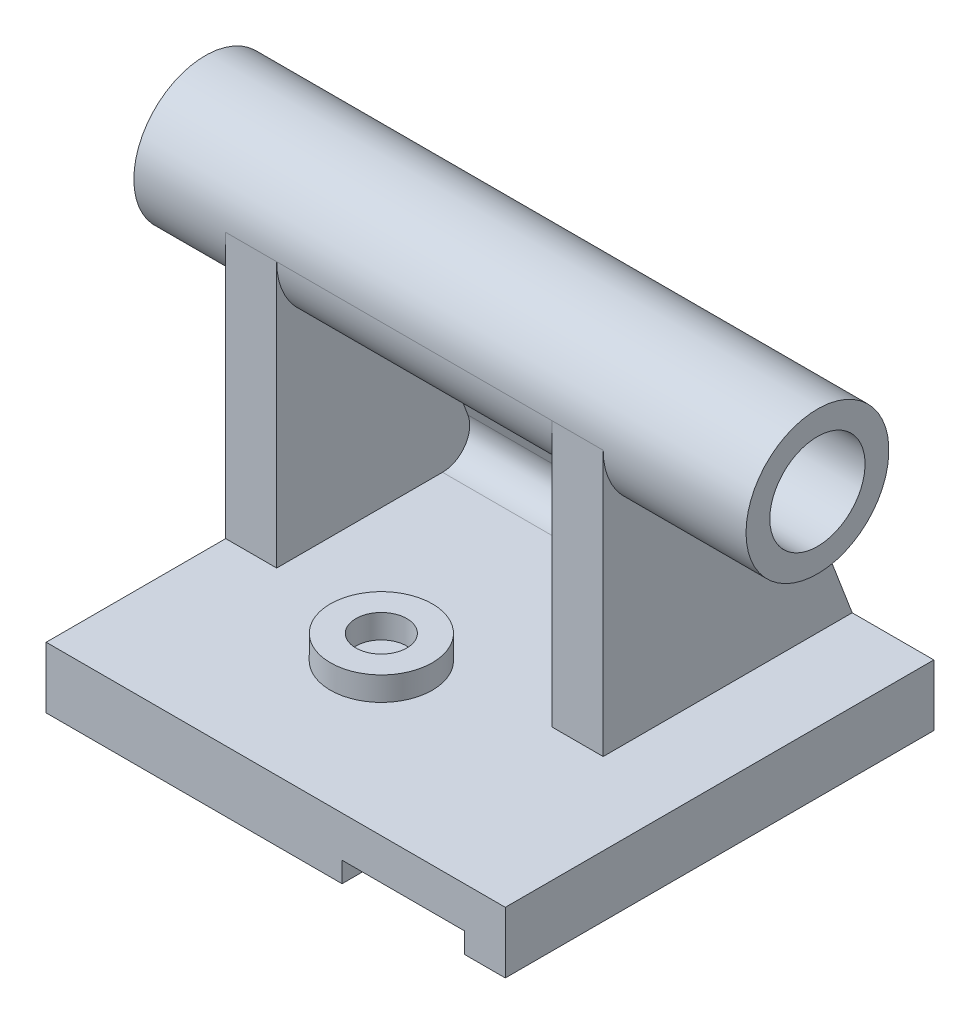
SolidWorks part; units mm, degrees
ref_plane "Front Plane" through (0, 0, 0) normal (0, 0, 1) x (1, 0, 0)
ref_plane "Top Plane" through (0, 0, 0) normal (0, 1, 0) x (1, 0, 0)
ref_plane "Right Plane" through (0, 0, 0) normal (1, 0, 0) x (0, 0, -1)
sketch "Sketch1" plane through (0, 0, 0) normal (0, 0, 1) x (1, 0, 0)
  line L0 (19.5, -9) -> (19.5, -3)
  line L1 (67.5, 9) -> (-67.5, 9)
  line L2 (67.5, 9) -> (67.5, -9)
  line L3 (67.5, -9) -> (55.5, -9)
  line L4 (-67.5, 9) -> (-67.5, -9)
  line L5 (67.5, 9) -> (-67.5, -9) construction
  line L6 (67.5, -9) -> (-67.5, 9) construction
  line L7 (19.5, -3) -> (55.5, -3)
  line L8 (55.5, -3) -> (55.5, -9)
  line L9 (19.5, -9) -> (-67.5, -9)
  point P0 (0, 0)
  dimension "D1" = 18
  dimension "D2" = 135
  dimension "D3" = 6
  dimension "D4" = 36
  dimension "D5" = 12
extrude "Boss-Extrude1" add sketch "Sketch1" along normal blind 126
sketch "Sketch2" plane through (-67.5, 0, 0) normal (-1, 0, 0) x (0, 0, 1)
  line L0 (73.219, 87) -> (73.219, 9)
  line L1 (126, 9) -> (0, 9) construction
  line L2 (32.5972, 94.4824) -> (0, 9)
  line L3 (33.3515, 62.7815) -> (16.9805, 19.8504)
  line L4 (126, 9) -> (24.4555, 9)
  line L6 (52.219, 66) -> (38.0234, 66)
  line L8 (43.8097, 90.2067) -> (11.2124, 4.7243) construction
  circle A0 centre (52.219, 87) radius 21
  circle A1 centre (52.219, 87) radius 14
  arc A2 (33.3515, 62.7815) -> (38.0234, 66) centre (38.0234, 61) cw
  arc A3 (24.4555, 9) -> (16.9805, 19.8504) centre (24.4555, 17) cw
  dimension "D1" = 42
  dimension "D2" = 28
  dimension "D5" = 5
  dimension "D6" = 8
  dimension "D4" = 96
  dimension "D3" = 12
extrude "Boss-Extrude4" add sketch "Sketch2" along normal blind 27 and the other way blind 153 separate body
sketch "Sketch3" plane through (-67.5, 0, 0) normal (-1, 0, 0) x (0, 0, 1)
  line L0 (73.219, 87) -> (73.219, 9)
  line L1 (126, 9) -> (0, 9) construction
  line L2 (52.219, 87) -> (52.219, 66)
  line L3 (52.219, 66) -> (38.0234, 66)
  line L4 (32.5972, 94.4824) -> (0, 9)
  line L5 (33.3515, 62.7815) -> (16.9805, 19.8504)
  line L6 (126, 9) -> (24.4555, 9)
  line L8 (43.8097, 90.2067) -> (11.2124, 4.7243) construction
  circle A0 centre (52.219, 87) radius 21 construction
  arc A1 (24.4555, 9) -> (16.9805, 19.8504) centre (24.4555, 17) cw
  arc A2 (33.3515, 62.7815) -> (38.0234, 66) centre (38.0234, 61) cw
  circle A3 centre (52.219, 87) radius 21
  line M6 (126, 9) -> (0, 9)
  dimension "D2" = 8
  dimension "D3" = 5
  dimension "D1" = 12
extrude "Boss-Extrude5" add sketch "Sketch3" against normal blind 15 contours A3 L3 A2 L5 A1 L0 M6
sketch "Sketch4" plane through (-67.5, 0, 0) normal (-1, 0, 0) x (0, 0, 1)
  line L0 (32.5972, 94.4824) -> (0, 9)
  line L1 (52.219, 66) -> (38.0234, 66) construction
  line L2 (24.4555, 9) -> (0, 9) construction
  line L3 (33.3515, 62.7815) -> (16.9805, 19.8504) construction
  line L4 (52.219, 66) -> (38.0234, 66)
  line L5 (24.4555, 9) -> (0, 9)
  line L6 (33.3515, 62.7815) -> (16.9805, 19.8504)
  circle A0 centre (52.219, 87) radius 21 construction
  arc A1 (38.0234, 66) -> (33.3515, 62.7815) centre (38.0234, 61) ccw construction
  arc A2 (16.9805, 19.8504) -> (24.4555, 9) centre (24.4555, 17) ccw construction
  circle A3 centre (52.219, 87) radius 21
  arc A4 (38.0234, 66) -> (33.3515, 62.7815) centre (38.0234, 61) ccw
  arc A5 (16.9805, 19.8504) -> (24.4555, 9) centre (24.4555, 17) ccw
  line M7 (52.219, 66) -> (38.0234, 66)
  arc M8 (38.0234, 66) -> (33.3515, 62.7815) centre (38.0234, 61) ccw
  line M9 (33.3515, 62.7815) -> (16.9805, 19.8504)
  arc M10 (16.9805, 19.8504) -> (24.4555, 9) centre (24.4555, 17) ccw
  line M11 (24.4555, 9) -> (0, 9)
ref_plane "Plane1" through (43.5, 0, 0) normal (-1, 0, 0) x (0, 0, 1)
sketch "Sketch7" plane through (43.5, 0, 0) normal (-1, 0, 0) x (0, 0, 1)
  line L0 (73.219, 87) -> (73.219, 9)
  line L1 (73.219, 9) -> (24.4555, 9)
  line L2 (33.3515, 62.7815) -> (16.9805, 19.8504) construction
  line L3 (52.219, 66) -> (38.0234, 66) construction
  line L4 (33.3515, 62.7815) -> (16.9805, 19.8504)
  line L5 (52.219, 66) -> (38.0234, 66)
  circle A0 centre (52.219, 87) radius 21 construction
  arc A1 (16.9805, 19.8504) -> (24.4555, 9) centre (24.4555, 17) ccw construction
  arc A2 (38.0234, 66) -> (33.3515, 62.7815) centre (38.0234, 61) ccw construction
  arc A3 (16.9805, 19.8504) -> (24.4555, 9) centre (24.4555, 17) ccw
  arc A4 (38.0234, 66) -> (33.3515, 62.7815) centre (38.0234, 61) ccw
  circle A5 centre (52.219, 87) radius 21
extrude "Boss-Extrude7" add sketch "Sketch7" along normal blind 15 contours A5 L5 A4 L4 A3 L1 L0
extrude "Boss-Extrude8" add sketch "Sketch4" against normal blind 111 contours A3 L0 M11 M10 M9 M8 M7
sketch "Sketch11" plane through (0, 9, 0) normal (0, 1, 0) x (1, 0, 0)
  circle A0 centre (-13.5, -81.444) radius 7.5
  circle A1 centre (-13.5, -81.444) radius 15
  dimension "D1" = 30
  dimension "D2" = 15
  dimension "D3" = 81
extrude "Boss-Extrude9" add sketch "Sketch11" along normal blind 7
